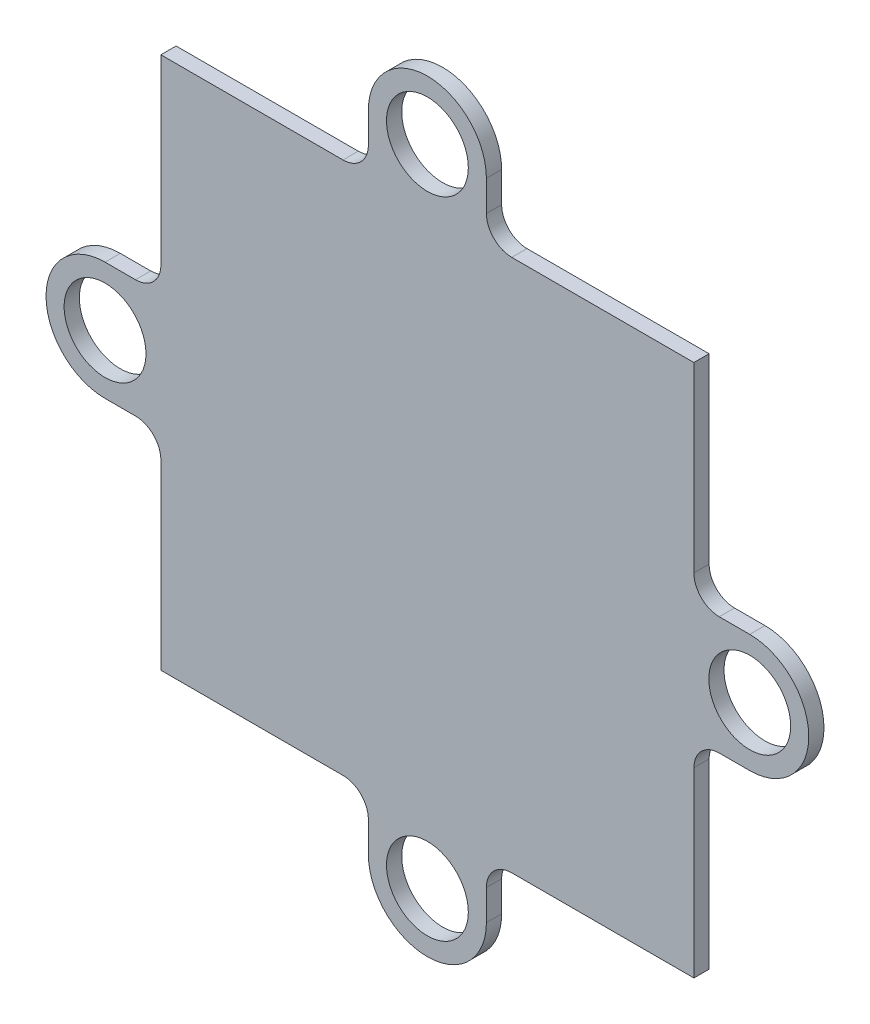
SolidWorks part; units mm, degrees
ref_plane "Front Plane" through (0, 0, 0) normal (0, 0, 1) x (1, 0, 0)
ref_plane "Top Plane" through (0, 0, 0) normal (0, 1, 0) x (1, 0, 0)
ref_plane "Right Plane" through (0, 0, 0) normal (1, 0, 0) x (0, 0, -1)
sketch "Sketch1" plane through (0, 0, 0) normal (0, 0, 1) x (1, 0, 0)
  line L0 (-4.65, 25.4) -> (-4.65, 23)
  line L1 (-21, -21) -> (-6.65, -21)
  line L2 (-21, -21) -> (-21, -6.65)
  line L3 (-21, 21) -> (-6.65, 21)
  line L4 (21, -21) -> (21, -6.65)
  line L5 (-21, -21) -> (21, 21) construction
  line L6 (-21, 21) -> (21, -21) construction
  line L7 (-6.65, 21) -> (-8.7591, 21)
  line L8 (4.65, 25.4) -> (4.65, 23)
  line L9 (6.65, 21) -> (7.1335, 21)
  line L10 (25.4, 4.65) -> (23, 4.65)
  line L11 (21, 6.65) -> (21, 8.7591)
  line L12 (25.4, -4.65) -> (23, -4.65)
  line L13 (21, -6.65) -> (21, -7.1335)
  line L14 (4.65, -25.4) -> (4.65, -23)
  line L15 (6.65, -21) -> (8.7591, -21)
  line L16 (-4.65, -25.4) -> (-4.65, -23)
  line L17 (-6.65, -21) -> (-7.1335, -21)
  line L18 (-25.4, -4.65) -> (-23, -4.65)
  line L19 (-21, -6.65) -> (-21, -8.7591)
  line L20 (-25.4, 4.65) -> (-23, 4.65)
  line L21 (-21, 6.65) -> (-21, 7.1335)
  line L22 (-21, 6.65) -> (-21, 21)
  line L23 (6.65, 21) -> (21, 21)
  line L24 (21, 6.65) -> (21, 21)
  line L25 (6.65, -21) -> (21, -21)
  circle A0 centre (0, 25.4) radius 3.225
  arc A1 (4.65, 25.4) -> (-4.65, 25.4) centre (0, 25.4) ccw
  arc A2 (4.65, 23) -> (6.65, 21) centre (6.65, 23) ccw
  arc A3 (-4.65, 23) -> (-6.65, 21) centre (-6.65, 23) cw
  circle A4 centre (25.4, 0) radius 3.225
  arc A5 (25.4, -4.65) -> (25.4, 4.65) centre (25.4, 0) ccw
  arc A6 (23, -4.65) -> (21, -6.65) centre (23, -6.65) ccw
  arc A7 (23, 4.65) -> (21, 6.65) centre (23, 6.65) cw
  circle A8 centre (0, -25.4) radius 3.225
  arc A9 (-4.65, -25.4) -> (4.65, -25.4) centre (0, -25.4) ccw
  arc A10 (-4.65, -23) -> (-6.65, -21) centre (-6.65, -23) ccw
  arc A11 (4.65, -23) -> (6.65, -21) centre (6.65, -23) cw
  circle A12 centre (-25.4, 0) radius 3.225
  arc A13 (-25.4, 4.65) -> (-25.4, -4.65) centre (-25.4, 0) ccw
  arc A14 (-23, 4.65) -> (-21, 6.65) centre (-23, 6.65) ccw
  arc A15 (-23, -4.65) -> (-21, -6.65) centre (-23, -6.65) cw
  point P0 (0, 0)
  point P53 (0, 0)
  dimension "D1" = 2
extrude "Boss-Extrude1" add sketch "Sketch1" along normal blind 1.2 contours L18 A15 L2 L1 A10 L16 A9 L14 A11 L15 L25 L4 A6 L12 A5 L10 A7 L11 L24 L23 L9 A2 L8 A1 L0 A3 L3 L22 L21 A14 L20 A13 A0 A4 A8 A12
